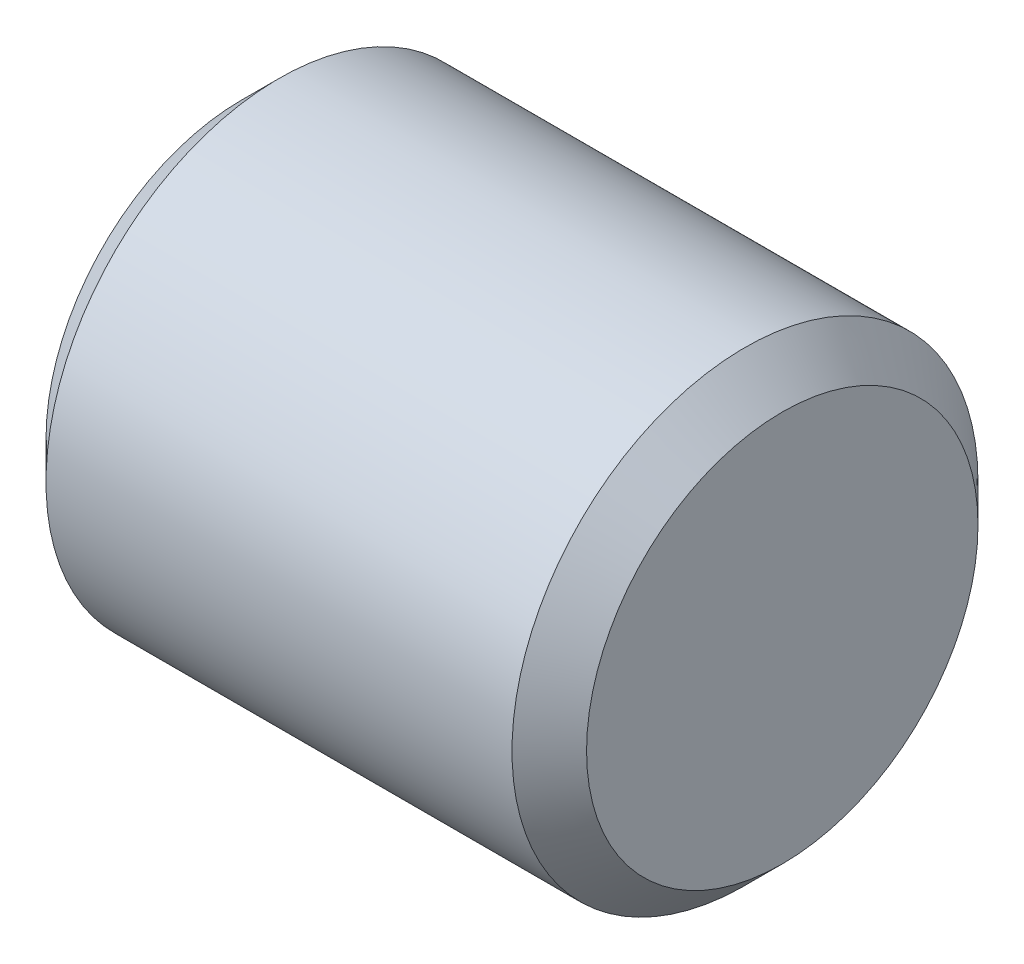
SolidWorks part; units mm, degrees
ref_plane "Front Plane" through (0, 0, 0) normal (0, 0, 1) x (1, 0, 0)
ref_plane "Top Plane" through (0, 0, 0) normal (0, 1, 0) x (1, 0, 0)
ref_plane "Right Plane" through (0, 0, 0) normal (1, 0, 0) x (0, 0, -1)
sketch "Sketch2" plane through (0, 0, 0) normal (1, 0, 0) x (0, 0, -1)
  circle A0 centre (0, 0) radius 7.9375
  dimension "D1" = 15.875
extrude "Boss-Extrude1" add sketch "Sketch2" along normal blind 18.415
chamfer "Chamfer1" distance 1.27 angle 45 2 edges at (18.415, 0, -7.9375) (0, 0, -7.9375)
sketch "Sketch3" plane through (18.415, 0, 0) normal (1, 0, 0) x (0, 0, -1)
  circle A0 centre (0, 0) radius 2.6221
sketch "Sketch4" plane through (0, 0, 0) normal (-1, 0, 0) x (0, 0, 1)
  line L0 (-2.8511, 1.397) -> (2.8511, 1.397)
  arc A0 (-2.8511, 1.397) -> (2.8511, 1.397) centre (0, 0) ccw
  dimension "D1" = 3.175
  dimension "D2" = 4.572
extrude "Cut-Extrude2" cut sketch "Sketch4" against normal offset from surface (15.24 mm away) 3.175 up to face at (18.415, 0, -6.6675)
sketch "Sketch5" plane through (0, 0, 0) normal (-1, 0, 0) x (0, 0, 1)
  circle A0 centre (0, 0) radius 3.81
  dimension "D1" = 7.62
extrude "Cut-Extrude3" cut sketch "Sketch5" against normal blind 3.175
